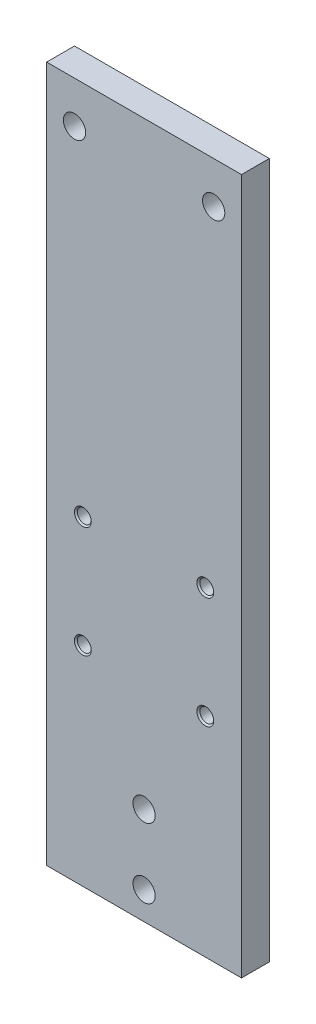
SolidWorks part; units mm, degrees
ref_plane "Front Plane" through (0, 0, 0) normal (0, 0, 1) x (1, 0, 0)
ref_plane "Top Plane" through (0, 0, 0) normal (0, 1, 0) x (1, 0, 0)
ref_plane "Right Plane" through (0, 0, 0) normal (1, 0, 0) x (0, 0, -1)
sketch "Sketch1" plane through (0, 0, 0) normal (0, 0, 1) x (1, 0, 0)
  line L0 (-25, 110) -> (25, 110) construction
  line L1 (-35, -125) -> (35, -125)
  line L2 (-35, -125) -> (-35, 125)
  line L3 (-35, 125) -> (35, 125)
  line L4 (35, -125) -> (35, 125)
  line L5 (-35, -125) -> (35, 125) construction
  line L6 (-35, 125) -> (35, -125) construction
  circle A0 centre (-25, 110) radius 4
  circle A1 centre (25, 110) radius 4
  point P0 (0, 0)
  point P10 (0, 110)
  dimension "D3" = 8
  dimension "D1" = 70
  dimension "D2" = 250
  dimension "D4" = 50
  dimension "D5" = 15
extrude "Boss-Extrude1" add sketch "Sketch1" along normal blind 10
sketch "Sketch2" plane through (0, 0, 10) normal (0, 0, 1) x (1, 0, 0)
  line L1 (-22, -50) -> (22, -50) construction
  line L2 (-22, -50) -> (-22, -10) construction
  line L3 (-22, -10) -> (22, -10) construction
  line L4 (22, -50) -> (22, -10) construction
  line L5 (-22, -50) -> (22, -10) construction
  line L6 (-22, -10) -> (22, -50) construction
  line L7 (-25, 110) -> (25, 110) construction
  point P0 (0, -30)
  dimension "D1" = 44
  dimension "D2" = 40
  dimension "D3" = 160
hole_wizard "M6x1.0 Tapped Hole2" positions "Sketch5" profile "Sketch6" tap size "M6x1.0" standard "ANSI Metric" end condition through all
sketch "Sketch5" plane through (0, 0, 10) normal (0, 0, 1) x (1, 0, 0)
  point P0 (-22, -10)
  point P3 (22, -10)
  point P6 (22, -50)
  point P9 (-22, -50)
sketch "Sketch6" plane through (-22, -10, 10) normal (1, 0, 0) x (0, -1, 0)
  line L0 (0, 0) -> (0, 10)
  line L1 (0, 10) -> (2.5, 10)
  line L2 (2.5, 10) -> (2.5, 0.525)
  line L3 (2.5, 0.525) -> (3.025, 0)
  line L5 (3.025, 0) -> (0, 0)
  line L6 (-2.5, 0.525) -> (-3.025, 0) construction
  line L11 (0, -6.35) -> (0, 107.95) construction
  dimension "Thru Tap Drill Dia." = 5
  dimension "Thru Tap Drill Depth" = 10
  dimension "Near C'Sink Dia." = 6.05
  dimension "Near C'Sink Angle" = 90
cosmetic thread "Hole Thread5" parameters "D2"=6
cosmetic thread "Hole Thread6" parameters "D2"=6
cosmetic thread "Hole Thread7" parameters "D2"=6
cosmetic thread "Hole Thread8" parameters "D2"=6
sketch "Sketch7" plane through (0, 0, 10) normal (0, 0, 1) x (1, 0, 0)
  line L0 (0, -90) -> (0, -115) construction
  line L1 (-35, -125) -> (35, -125) construction
  circle A0 centre (0, -90) radius 4
  circle A1 centre (0, -115) radius 4
  dimension "D2" = 8
  dimension "D1" = 25
  dimension "D3" = 10
extrude "Cut-Extrude1" cut sketch "Sketch7" against normal through all
